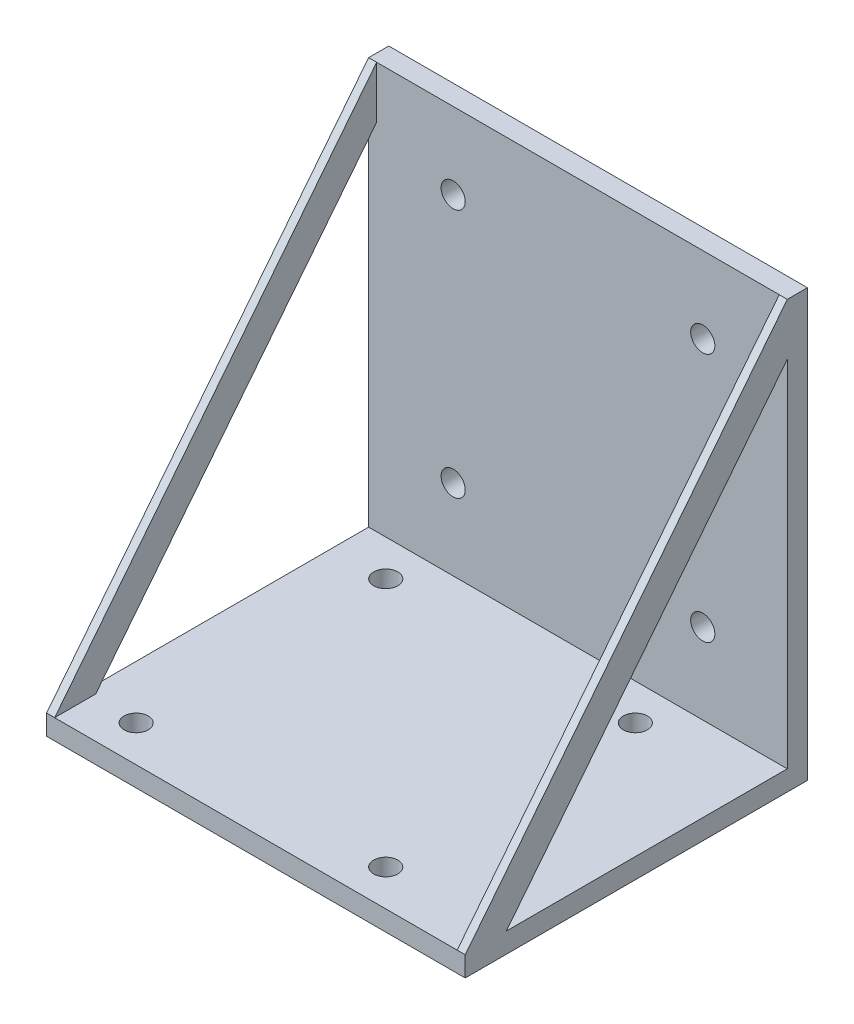
SolidWorks part; units mm, degrees
ref_plane "Front Plane" through (0, 0, 0) normal (0, 0, 1) x (1, 0, 0)
ref_plane "Top Plane" through (0, 0, 0) normal (0, 1, 0) x (1, 0, 0)
ref_plane "Right Plane" through (0, 0, 0) normal (1, 0, 0) x (0, 0, -1)
sketch "Sketch1" plane through (0, 0, 0) normal (0, 0, 1) x (1, 0, 0)
  line L1 (-25, -25) -> (25, -25) construction
  line L2 (-25, -25) -> (-25, 25)
  line L3 (-25, 25) -> (25, 25)
  line L4 (25, -25) -> (25, 25)
  line L5 (-25, -25) -> (25, 25) construction
  line L6 (-25, 25) -> (25, -25) construction
  line L8 (-25, -25) -> (-25, -28)
  line L9 (-25, -28) -> (25, -28)
  line L10 (25, -25) -> (25, -28)
  circle A0 centre (-15.5, 15.5) radius 1.5
  circle A1 centre (15.5, 15.5) radius 1.5
  circle A2 centre (15.5, -15.5) radius 1.5
  circle A3 centre (-15.5, -15.5) radius 1.5
  point P0 (0, 0)
  dimension "D3" = 3
  dimension "D1" = 50
  dimension "D2" = 50
  dimension "D4" = 15.5
  dimension "D5" = 3
extrude "Boss-Extrude1" add sketch "Sketch1" along normal blind 2.5
sketch "Sketch2" plane through (0, 0, 2.5) normal (0, 0, 1) x (1, 0, 0)
  line L0 (25, -28) -> (25, 25) construction
  line L1 (-25, -28) -> (25, -28)
  line L2 (-25, -28) -> (-25, -25.5)
  line L3 (-25, -25.5) -> (25, -25.5)
  line L4 (25, -28) -> (25, -25.5)
  dimension "D1" = 2.5
extrude "Boss-Extrude2" add sketch "Sketch2" along normal blind 40
sketch "Sketch3" plane through (0, -25.5, 0) normal (0, 1, 0) x (1, 0, 0)
  line L0 (-25, -2.5) -> (25, -42.5) construction
  line L1 (-25, -42.5) -> (25, -2.5) construction
  circle A0 centre (-19.375, -7) radius 1.5
  circle A1 centre (11.625, -7) radius 1.5
  circle A2 centre (11.625, -38) radius 1.5
  circle A3 centre (-19.375, -38) radius 1.5
  point P10 (0, -22.5)
  dimension "D1" = 3
  dimension "D2" = 15.5
extrude "Cut-Extrude1" cut sketch "Sketch3" against normal blind 40
sketch "Sketch5" plane through (25, 0, 0) normal (1, 0, 0) x (0, 0, -1)
  line L0 (-42.5, -25.5) -> (-2.5, 25)
  line L1 (-2.5, 25) -> (0, 25)
  line L2 (0, 25) -> (0, 16.8431)
  line L3 (0, -28) -> (0, 25) construction
  line L4 (-2.5, 18.5578) -> (-37.3972, -25.5)
  line L5 (-42.5, -28) -> (0, -28) construction
  line L6 (-39.3431, -28) -> (-42.5, -28)
  line L7 (-42.5, -28) -> (-42.5, -25.5)
  line L8 (-39.3431, -28) -> (0, -28)
  line L9 (0, -28) -> (0, 16.8431)
  line L10 (-2.5, 18.5578) -> (-2.5, -25.5)
  line L11 (-2.5, -25.5) -> (-2.5, 25) construction
  line L12 (-2.5, -25.5) -> (-37.3972, -25.5)
  line L13 (-42.5, -25.5) -> (-2.5, -25.5) construction
  dimension "D1" = 4
extrude "Boss-Extrude3" add sketch "Sketch5" along normal blind 1
mirror "Mirror1" about plane through (0, 0, 0) normal (1, 0, 0) of "Boss-Extrude3"
